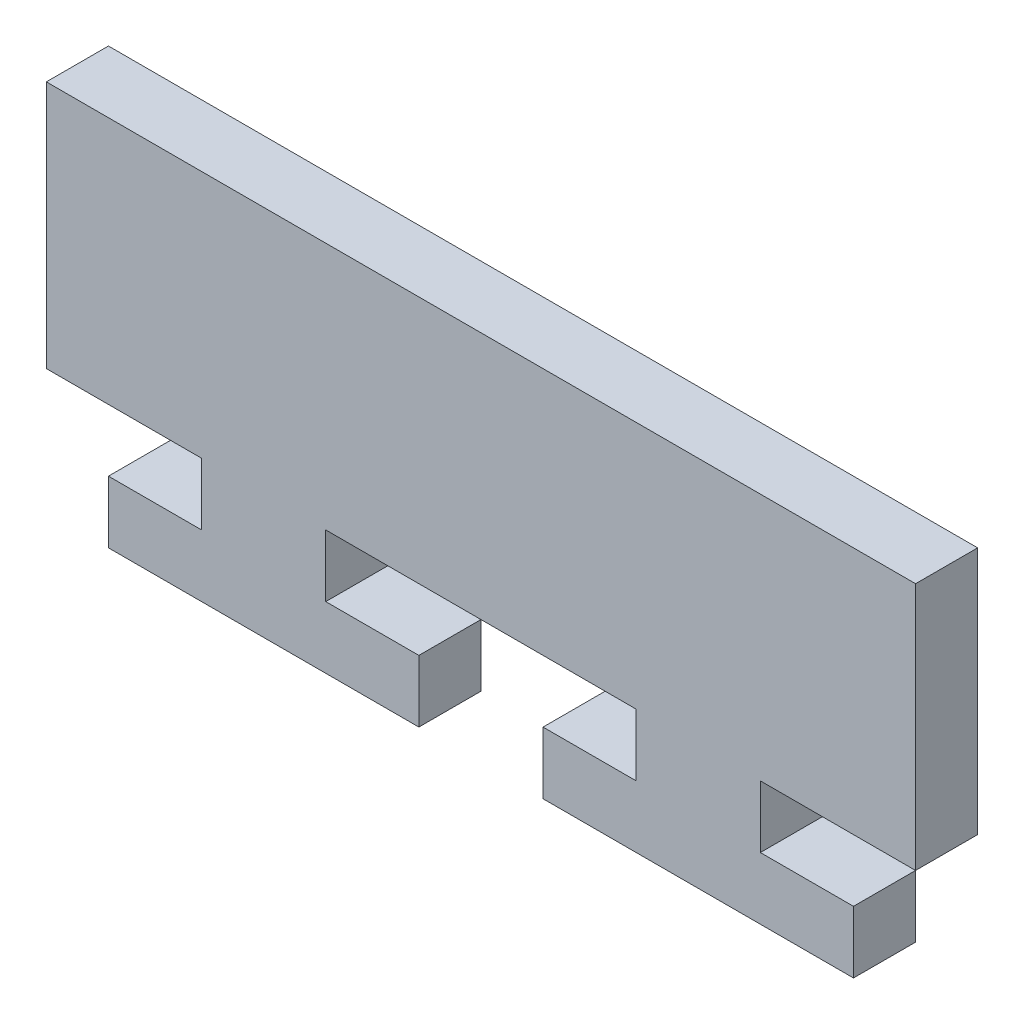
SolidWorks part; units mm, degrees
ref_plane "Plan de face" through (0, 0, 0) normal (0, 0, 1) x (1, 0, 0)
ref_plane "Plan de dessus" through (0, 0, 0) normal (0, 1, 0) x (1, 0, 0)
ref_plane "Plan de droite" through (0, 0, 0) normal (1, 0, 0) x (0, 0, -1)
sketch "Esquisse1" plane through (0, 0, 0) normal (0, 0, 1) x (1, 0, 0)
  line L0 (-35, -10) -> (-22.5, -10)
  line L1 (-35, 10) -> (35, 10)
  line L2 (-35, 10) -> (-35, -10)
  line L3 (-35, -10) -> (35, -10) construction
  line L4 (35, 10) -> (35, -10)
  line L5 (-22.5, -10) -> (-22.5, -15)
  line L6 (-22.5, -15) -> (-30, -15)
  line L7 (-30, -15) -> (-30, -20)
  line L8 (-30, -20) -> (-5, -20)
  line L9 (-5, -20) -> (-5, -15)
  line L10 (-5, -15) -> (-12.5, -15)
  line L11 (-12.5, -15) -> (-12.5, -10)
  line L12 (-12.5, -10) -> (12.5, -10)
  line L13 (12.5, -10) -> (12.5, -15)
  line L14 (12.5, -15) -> (5, -15)
  line L15 (5, -15) -> (5, -20)
  line L16 (5, -20) -> (30, -20)
  line L17 (30, -20) -> (30, -15)
  line L18 (30, -15) -> (22.5, -15)
  line L19 (22.5, -15) -> (22.5, -10)
  line L20 (22.5, -10) -> (35, -10)
  dimension "D1" = 70
  dimension "D2" = 35
  dimension "D3" = 20
  dimension "D4" = 10
  dimension "D5" = 25
  dimension "D6" = 12.5
  dimension "D7" = 7.5
  dimension "D8" = 5
  dimension "D9" = 5
  dimension "D10" = 5
  dimension "D11" = 7.5
  dimension "D12" = 25
  dimension "D13" = 25
  dimension "D14" = 7.5
  dimension "D15" = 7.5
  dimension "D16" = 5
  dimension "D17" = 5
  dimension "D18" = 5
extrude "Boss.-Extru.1" add sketch "Esquisse1" along normal blind 5
